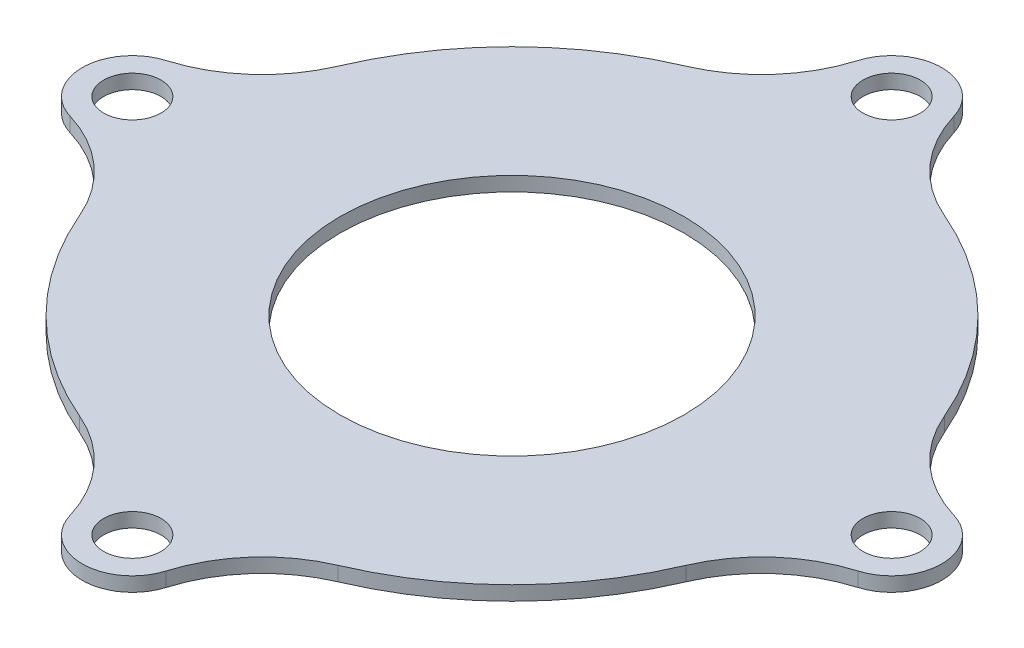
SolidWorks part; units mm, degrees
ref_plane "Front Plane" through (0, 0, 0) normal (0, 0, 1) x (1, 0, 0)
ref_plane "Top Plane" through (0, 0, 0) normal (0, 1, 0) x (1, 0, 0)
ref_plane "Right Plane" through (0, 0, 0) normal (1, 0, 0) x (0, 0, -1)
sketch "Sketch1" plane through (0, 0, 0) normal (0, 1, 0) x (1, 0, 0)
  circle A0 centre (0, 0) radius 23
  dimension "D1" = 46
extrude "Boss-Extrude1" add sketch "Sketch1" along normal blind 3 contours A0
sketch "Sketch2" plane through (0, 0, 0) normal (0, -1, 0) x (1, 0, 0)
  circle A0 centre (0, 0) radius 12
  dimension "D1" = 24
extrude "Cut-Extrude1" cut sketch "Sketch2" against normal blind 10
sketch "Sketch3" plane through (0, 0, 0) normal (0, -1, 0) x (1, 0, 0)
  line L0 (-30, 0) -> (30, 0) construction
  line L1 (0, 30) -> (0, -30) construction
  line L4 (-26.5, 3.5) -> (-22.7321, 3.5)
  line L5 (-26.5, -3.5) -> (-22.7321, -3.5)
  line L6 (3.5, 26.5) -> (3.5, 22.7321)
  line L7 (-3.5, 26.5) -> (-3.5, 22.7321)
  line L8 (26.5, -3.5) -> (22.7321, -3.5)
  line L9 (26.5, 3.5) -> (22.7321, 3.5)
  line L10 (-3.5, -26.5) -> (-3.5, -22.7321)
  line L11 (3.5, -26.5) -> (3.5, -22.7321)
  arc A2 (-26.5, 3.5) -> (-26.5, -3.5) centre (-26.5, 0) ccw
  circle A3 centre (0, 0) radius 23 construction
  arc A4 (-22.7321, 3.5) -> (-22.7321, -3.5) centre (0, 0) ccw
  arc A5 (3.5, 26.5) -> (-3.5, 26.5) centre (0, 26.5) ccw
  arc A6 (3.5, 22.7321) -> (-3.5, 22.7321) centre (0, 0) ccw
  arc A7 (26.5, -3.5) -> (26.5, 3.5) centre (26.5, 0) ccw
  arc A8 (22.7321, -3.5) -> (22.7321, 3.5) centre (0, 0) ccw
  arc A9 (-3.5, -26.5) -> (3.5, -26.5) centre (0, -26.5) ccw
  arc A10 (-3.5, -22.7321) -> (3.5, -22.7321) centre (0, 0) ccw
  circle A11 centre (0, 26.5) radius 1.75
  circle A12 centre (26.5, 0) radius 1.75
  circle A13 centre (0, -26.5) radius 1.75
  circle A14 centre (-26.5, 0) radius 1.75
  point P5 (0, 0)
  point P6 (0, 0)
  point P34 (0, 0)
  point P42 (0, 0)
  dimension "D2" = 7
  dimension "D3" = 4
  dimension "D4" = 3.5
  dimension "D1" = 60
  dimension "D5" = 4
extrude "Boss-Extrude2" add sketch "Sketch3" against normal blind 3
sketch "Sketch4" plane through (0, 0, 0) normal (0, -1, 0) x (1, 0, 0)
  circle A0 centre (-26.5, 0) radius 2.8
  circle A1 centre (0, 26.5) radius 2.8
  circle A2 centre (26.5, 0) radius 2.8
  circle A3 centre (0, -26.5) radius 2.8
  point P12 (0, 0)
  dimension "D1" = 5.6
  dimension "D2" = 4
extrude "Cut-Extrude2" cut sketch "Sketch4" against normal blind 1
fillet "Fillet1" radius 10 8 edges at (3.5, 1.5, 22.7321) (22.7321, 1.5, 3.5) (22.7321, 1.5, -3.5) (3.5, 1.5, -22.7321) (-3.5, 1.5, -22.7321) (-22.7321, 1.5, -3.5) (-22.7321, 1.5, 3.5) (-3.5, 1.5, 22.7321)
sketch "Sketch5" plane through (0, 3, 0) normal (0, 1, 0) x (1, 0, 0)
  circle A0 centre (0, 0) radius 31.1235
extrude "Cut-Extrude3" cut sketch "Sketch5" against normal offset from surface (1 mm away) 2 up to face at (-26.5, 0, -2.8)
sketch "Sketch6" plane through (0, 2, 0) normal (0, 1, 0) x (1, 0, 0)
  arc A16 (3.354, 27.5003) -> (9.0166, 21.1589) centre (12.9368, 30.3585) ccw
  arc A17 (3.354, 27.5003) -> (-3.354, 27.5003) centre (0, 26.5) ccw
  arc A18 (-9.0166, 21.1589) -> (-3.354, 27.5003) centre (-12.9368, 30.3585) ccw
  arc A19 (-9.0166, 21.1589) -> (-21.1589, 9.0166) centre (0, 0) ccw
  arc A20 (-27.5003, 3.354) -> (-21.1589, 9.0166) centre (-30.3585, 12.9368) ccw
  arc A21 (-27.5003, 3.354) -> (-27.5003, -3.354) centre (-26.5, 0) ccw
  arc A22 (-21.1589, -9.0166) -> (-27.5003, -3.354) centre (-30.3585, -12.9368) ccw
  arc A23 (-21.1589, -9.0166) -> (-9.0166, -21.1589) centre (0, 0) ccw
  arc A24 (-3.354, -27.5003) -> (-9.0166, -21.1589) centre (-12.9368, -30.3585) ccw
  arc A25 (-3.354, -27.5003) -> (3.354, -27.5003) centre (0, -26.5) ccw
  arc A26 (9.0166, -21.1589) -> (3.354, -27.5003) centre (12.9368, -30.3585) ccw
  arc A27 (9.0166, -21.1589) -> (21.1589, -9.0166) centre (0, 0) ccw
  arc A28 (27.5003, -3.354) -> (21.1589, -9.0166) centre (30.3585, -12.9368) ccw
  arc A29 (27.5003, -3.354) -> (27.5003, 3.354) centre (26.5, 0) ccw
  arc A30 (21.1589, 9.0166) -> (27.5003, 3.354) centre (30.3585, 12.9368) ccw
  arc A31 (21.1589, 9.0166) -> (9.0166, 21.1589) centre (0, 0) ccw
  arc A32 (3.354, 27.5003) -> (9.0166, 21.1589) centre (12.9368, 30.3585) ccw
  arc A33 (3.354, 27.5003) -> (-3.354, 27.5003) centre (0, 26.5) ccw
  arc A34 (-9.0166, 21.1589) -> (-3.354, 27.5003) centre (-12.9368, 30.3585) ccw
  arc A35 (-9.0166, 21.1589) -> (-21.1589, 9.0166) centre (0, 0) ccw
  arc A36 (-27.5003, 3.354) -> (-21.1589, 9.0166) centre (-30.3585, 12.9368) ccw
  arc A37 (-27.5003, 3.354) -> (-27.5003, -3.354) centre (-26.5, 0) ccw
  arc A38 (-21.1589, -9.0166) -> (-27.5003, -3.354) centre (-30.3585, -12.9368) ccw
  arc A39 (-21.1589, -9.0166) -> (-9.0166, -21.1589) centre (0, 0) ccw
  arc A40 (-3.354, -27.5003) -> (-9.0166, -21.1589) centre (-12.9368, -30.3585) ccw
  arc A41 (-3.354, -27.5003) -> (3.354, -27.5003) centre (0, -26.5) ccw
  arc A42 (9.0166, -21.1589) -> (3.354, -27.5003) centre (12.9368, -30.3585) ccw
  arc A43 (9.0166, -21.1589) -> (21.1589, -9.0166) centre (0, 0) ccw
  arc A44 (27.5003, -3.354) -> (21.1589, -9.0166) centre (30.3585, -12.9368) ccw
  arc A45 (27.5003, -3.354) -> (27.5003, 3.354) centre (26.5, 0) ccw
  arc A46 (21.1589, 9.0166) -> (27.5003, 3.354) centre (30.3585, 12.9368) ccw
  arc A47 (21.1589, 9.0166) -> (9.0166, 21.1589) centre (0, 0) ccw
  dimension "D1" = 0
extrude "Cut-Extrude4" cut sketch "Sketch6" against normal offset from surface (1 mm away) 1 up to face at (0, 2, 0)
sketch "Sketch7" plane through (0, 0, 0) normal (0, -1, 0) x (1, 0, 0)
  circle A0 centre (0, 26.5) radius 2.8
  circle A1 centre (0, 26.5) radius 2
  circle A2 centre (26.5, 0) radius 2.8
  circle A3 centre (26.5, 0) radius 2
  circle A4 centre (0, -26.5) radius 2.8
  circle A5 centre (0, -26.5) radius 2
  circle A6 centre (-26.5, 0) radius 2.8
  circle A7 centre (-26.5, 0) radius 2
  point P16 (0, 0)
  dimension "D1" = 4
  dimension "D2" = 4
extrude "Boss-Extrude3" add sketch "Sketch7" against normal blind 1
